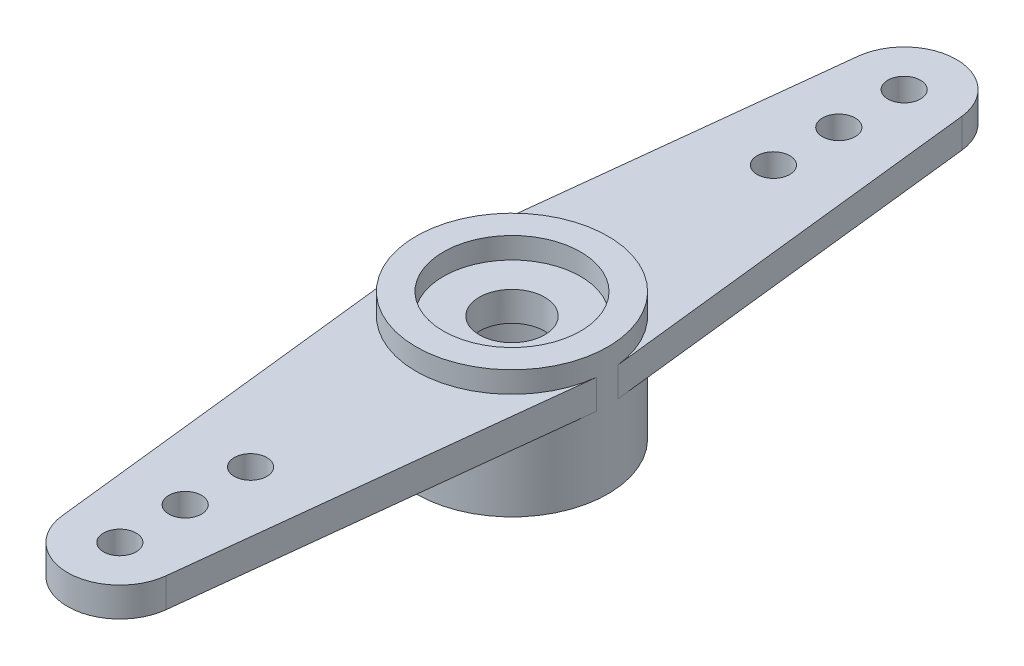
SolidWorks part; units mm, degrees
ref_plane "Front Plane" through (0, 0, 0) normal (0, 0, 1) x (1, 0, 0)
ref_plane "Top Plane" through (0, 0, 0) normal (0, 1, 0) x (1, 0, 0)
ref_plane "Right Plane" through (0, 0, 0) normal (1, 0, 0) x (0, 0, -1)
sketch "Sketch1" plane through (0, 0, 0) normal (0, 1, 0) x (1, 0, 0)
  circle A0 centre (0, 0) radius 2.935
  dimension "D1" = 5.87
extrude "Boss-Extrude2" add sketch "Sketch1" along normal blind 3.25
sketch "Sketch2" plane through (0, 3.25, 0) normal (0, 1, 0) x (1, 0, 0)
  line L0 (0, 0) -> (0, 10.5)
  line L1 (-1.5901, 12.178) -> (-2.9168, 0.3265)
  line L2 (1.5901, 12.178) -> (2.9168, 0.3265)
  line L3 (0, 0) -> (7.6627, 0)
  line L4 (1.5901, -12.178) -> (2.9168, -0.3265)
  line L5 (-1.5901, -12.178) -> (-2.9168, -0.3265)
  line L6 (0, 11.5) -> (0, 12)
  arc A0 (1.5901, 12.178) -> (-1.5901, 12.178) centre (0, 12) ccw
  circle A1 centre (0, 12) radius 0.5
  circle A2 centre (0, 0) radius 2.935
  circle A3 centre (0, 0) radius 2.935
  circle A4 centre (0, 10) radius 0.5
  circle A5 centre (0, 8) radius 0.5
  circle A6 centre (0, -8) radius 0.5
  circle A7 centre (0, -10) radius 0.5
  circle A8 centre (0, -12) radius 0.5
  arc A9 (1.5901, -12.178) -> (-1.5901, -12.178) centre (0, -12) cw
  arc A10 (-0.2674, -10.4225) -> (0.2674, -10.4225) centre (0, -12) cw
  arc A11 (-0.2674, 10.4225) -> (0.2674, 10.4225) centre (0, 12) ccw
  dimension "D1" = 3.2
  dimension "D4" = 1
  dimension "D5" = 1
  dimension "D6" = 1
  dimension "D2" = 12
  dimension "D7" = 2
  dimension "D8" = 2
  dimension "D3" = 0
extrude "Boss-Extrude3" add sketch "Sketch2" against normal blind 0.9
sketch "Sketch3" plane through (0, 3.25, 0) normal (0, 1, 0) x (1, 0, 0)
  circle A1 centre (0, 0) radius 2.935
  circle A2 centre (0, 0) radius 2.935
  dimension "D1" = 0
extrude "Boss-Extrude4" add sketch "Sketch3" along normal blind 0.65
sketch "Sketch4" plane through (0, 3.9, 0) normal (0, 1, 0) x (1, 0, 0)
  circle A0 centre (0, 0) radius 2.1
  dimension "D1" = 4.2
extrude "Cut-Extrude1" cut sketch "Sketch4" against normal blind 0.65
sketch "Sketch5" plane through (0, 3.25, 0) normal (0, 1, 0) x (1, 0, 0)
  circle A0 centre (0, 0) radius 1
  dimension "D1" = 2
extrude "Cut-Extrude2" cut sketch "Sketch5" against normal blind 5.65
sketch "Sketch6" plane through (0, 0, 0) normal (0, -1, 0) x (1, 0, 0)
  circle A0 centre (0, 0) radius 2.1 construction
  circle A1 centre (0, 0) radius 2.1
extrude "Cut-Extrude3" cut sketch "Sketch6" against normal blind 2.35
